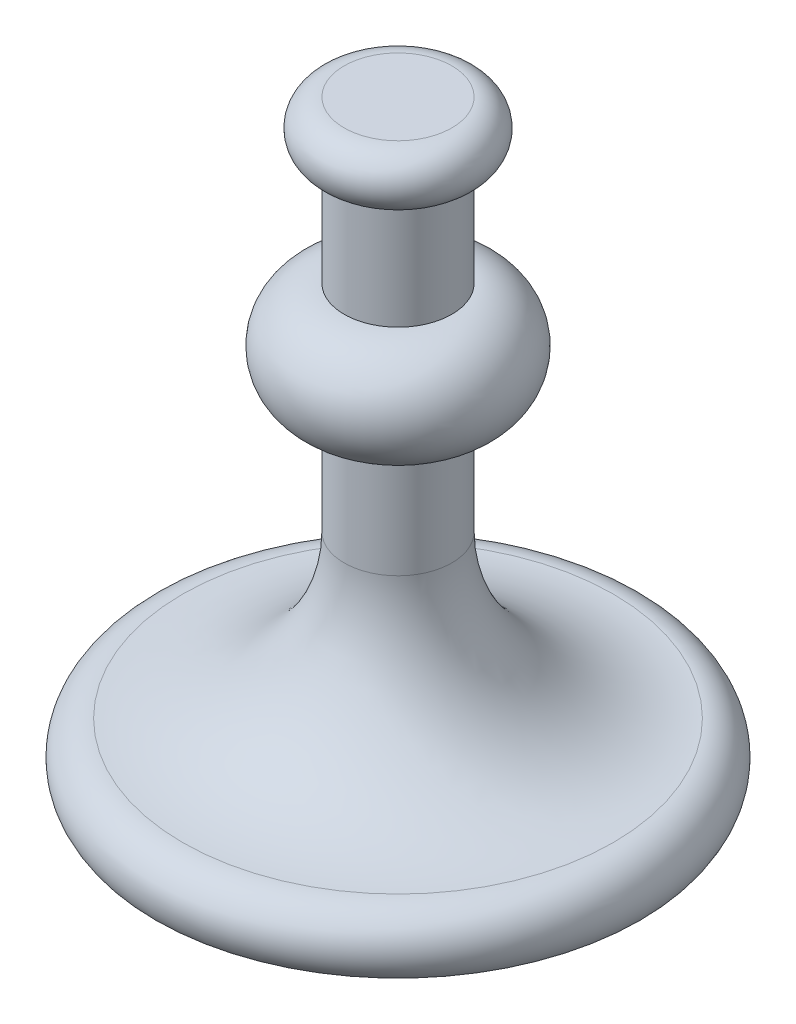
SolidWorks part; units mm, degrees
ref_plane "Front Plane" through (0, 0, 0) normal (0, 0, 1) x (1, 0, 0)
ref_plane "Top Plane" through (0, 0, 0) normal (0, 1, 0) x (1, 0, 0)
ref_plane "Right Plane" through (0, 0, 0) normal (1, 0, 0) x (0, 0, -1)
other "Sketch3"
sketch "Sketch1" plane through (0, 0, 0) normal (0, 0, 1) x (1, 0, 0)
  line L0 (0, 0) -> (0, 220)
  line L1 (0, 220) -> (20, 220)
  line L2 (0, 0) -> (90, 0)
  line L3 (20, 200) -> (20, 160)
  line L4 (20, 120) -> (20, 80.0013)
  line L5 (0, 220) -> (0, 321.415) construction
  arc A0 (20, 220) -> (20, 200) centre (20, 210) cw
  arc A1 (20, 160) -> (20, 120) centre (20, 140) cw
  arc A2 (20, 80.0013) -> (80, 20.0013) centre (80, 80.0013) ccw
  arc A3 (80, 20.0013) -> (90, 0) centre (80, 7.5008) cw
  point P14 (0, 80.0013)
  point P15 (20, 0)
  dimension "D4" = 10
  dimension "D6" = 60
  dimension "D7" = 12.5005
  dimension "D1" = 220
  dimension "D2" = 20
  dimension "D3" = 90
  dimension "D5" = 40
  dimension "D8" = 80.0013
revolve "Revolve1" add sketch "Sketch1" angle 360 about L5
